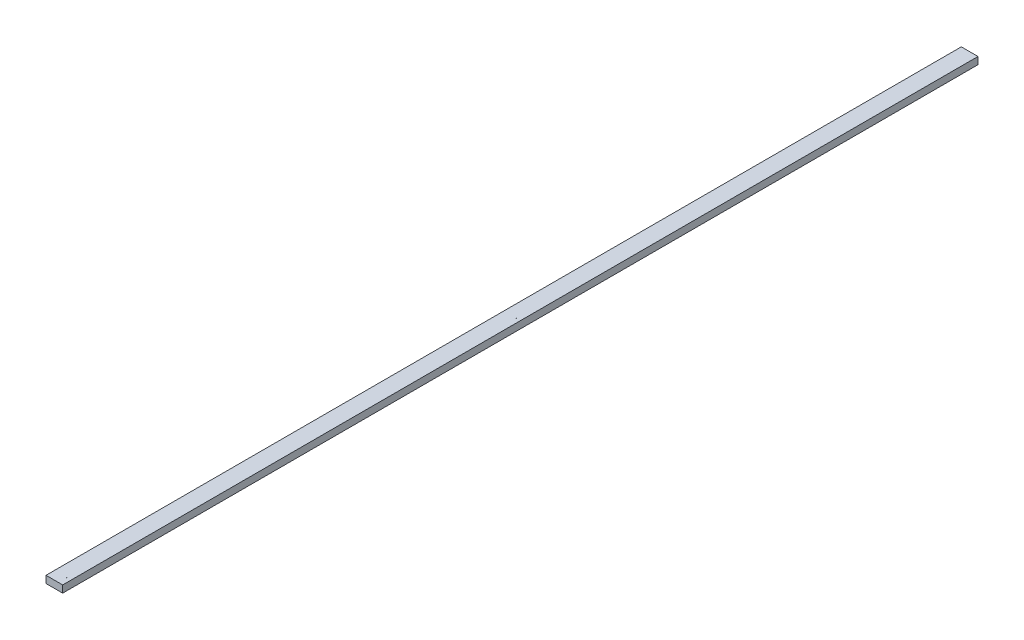
SolidWorks part; units mm, degrees
material "Pine"
ref_plane "Front Plane" through (0, 0, 0) normal (0, 0, 1) x (1, 0, 0)
ref_plane "Top Plane" through (0, 0, 0) normal (0, 1, 0) x (1, 0, 0)
ref_plane "Right Plane" through (0, 0, 0) normal (1, 0, 0) x (0, 0, -1)
sketch "Sketch1" plane through (0, 0, 0) normal (0, 0, 1) x (1, 0, 0)
  line L1 (0, 0) -> (88.9, 0)
  line L2 (0, 0) -> (0, 38.1)
  line L3 (0, 38.1) -> (88.9, 38.1)
  line L4 (88.9, 0) -> (88.9, 38.1)
  dimension "D1" = 88.9
  dimension "D2" = 38.1
extrude "Boss-Extrude1" add sketch "Sketch1" along normal blind 4876.8
sketch "Sketch3" plane through (0, 38.1, 0) normal (0, 1, 0) x (1, 0, 0)
  line L0 (88.9, -44.45) -> (44.45, -44.45) construction
  line L2 (44.45, -44.45) -> (0, -44.45) construction
  line L3 (88.9, -2438.4) -> (44.45, -2438.4) construction
  line L6 (88.9, -4876.8) -> (88.9, 0) construction
  line L7 (44.45, -2438.4) -> (0, -2438.4) construction
  line L8 (0, -4876.8) -> (0, 0) construction
  line L9 (88.9, 0) -> (0, 0) construction
  circle A0 centre (66.675, -2438.4) radius 0.8763
  circle A1 centre (22.225, -2438.4) radius 0.8763
  circle A2 centre (66.675, -44.45) radius 0.8763
  circle A3 centre (22.225, -44.45) radius 0.8763
  circle A4 centre (22.225, -4832.35) radius 0.8763
  circle A5 centre (66.675, -4832.35) radius 0.8763
  dimension "D2" = 1.7526
  dimension "D3" = 1.7526
  dimension "D1" = 44.45
extrude "Cut-Extrude2" cut sketch "Sketch3" against normal up to surface (38.1 mm away) up to face at (44.45, 0, 2438.4)
equation "\"length\"= 1219.2 * 4"
equation "\"D1@Boss-Extrude1\"=\"length\""
